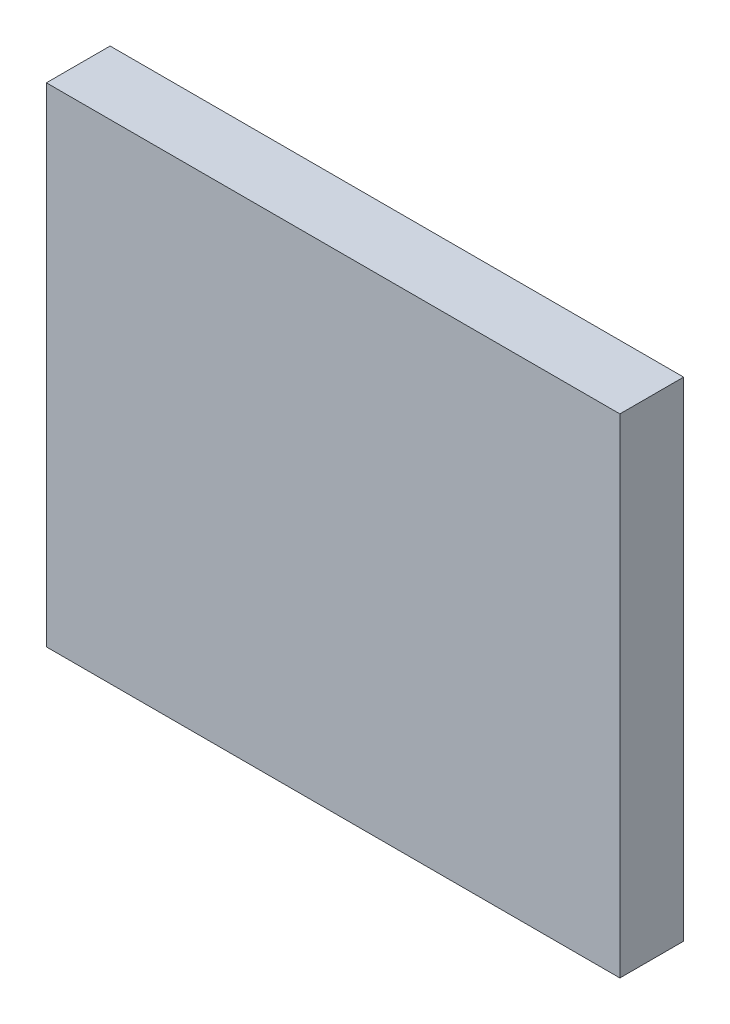
SolidWorks part; units mm, degrees
ref_plane "Plan de face" through (0, 0, 0) normal (0, 0, 1) x (1, 0, 0)
ref_plane "Plan de dessus" through (0, 0, 0) normal (0, 1, 0) x (1, 0, 0)
ref_plane "Plan de droite" through (0, 0, 0) normal (1, 0, 0) x (0, 0, -1)
sketch "Esquisse1" plane through (0, 0, 0) normal (0, 0, 1) x (1, 0, 0)
  line L1 (-13.5, -11.5) -> (13.5, -11.5)
  line L2 (-13.5, -11.5) -> (-13.5, 11.5)
  line L3 (-13.5, 11.5) -> (13.5, 11.5)
  line L4 (13.5, -11.5) -> (13.5, 11.5)
  line L5 (-13.5, -11.5) -> (13.5, 11.5) construction
  line L6 (-13.5, 11.5) -> (13.5, -11.5) construction
  point P0 (0, 0)
  dimension "D1" = 27
  dimension "D2" = 23
extrude "Boss.-Extru.1" add sketch "Esquisse1" along normal blind 3
